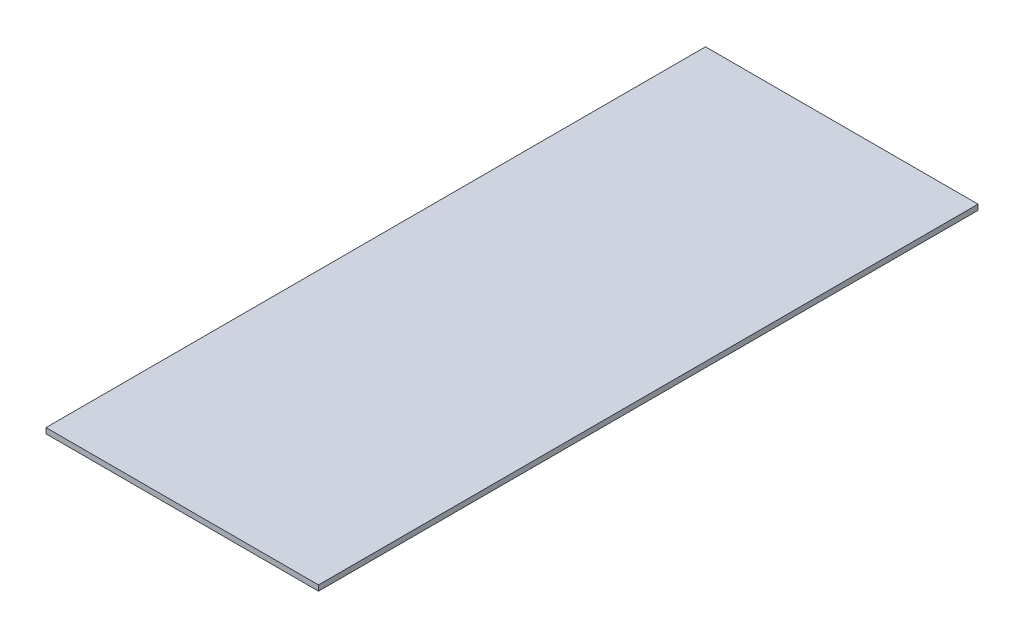
SolidWorks part; units mm, degrees
ref_plane "前视基准面" through (0, 0, 0) normal (0, 0, 1) x (1, 0, 0)
ref_plane "上视基准面" through (0, 0, 0) normal (0, 1, 0) x (1, 0, 0)
ref_plane "右视基准面" through (0, 0, 0) normal (1, 0, 0) x (0, 0, -1)
sketch "草图2" plane through (0, 0, 0) normal (0, 1, 0) x (1, 0, 0)
  line L2 (0, 121) -> (50, 121)
  line L3 (50, 121) -> (50, -121)
  line L4 (50, -121) -> (-50, -121)
  line L5 (-50, -121) -> (-50, 121)
  line L6 (-50, 121) -> (0, 121)
extrude "凸台-拉伸1" add sketch "草图2" along normal blind 2
